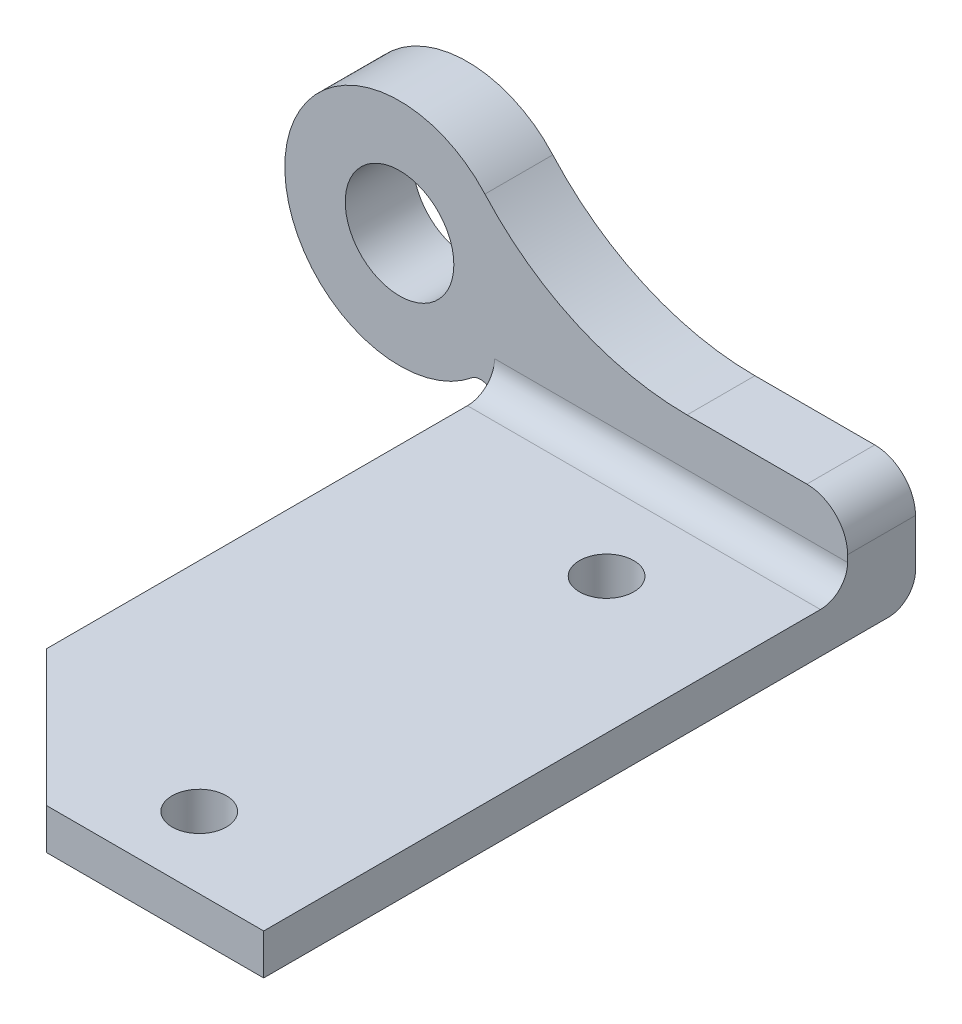
SolidWorks part; units mm, degrees
material "6061 合金"
ref_plane "前视基准面" through (0, 0, 0) normal (0, 0, 1) x (1, 0, 0)
ref_plane "上视基准面" through (0, 0, 0) normal (0, 1, 0) x (1, 0, 0)
ref_plane "右视基准面" through (0, 0, 0) normal (1, 0, 0) x (0, 0, -1)
sketch "草图1" plane through (0, 0, 0) normal (0, 0, 1) x (1, 0, 0)
  line L0 (-5.4584, -21.0602) -> (-5.4584, -21.2593)
  line L1 (-5.4584, -21.2593) -> (20.5416, -21.2593)
  line L2 (20.5416, -21.2593) -> (20.5416, -17.7593)
  line L3 (17.5416, -14.7593) -> (8.7172, -14.7593)
  line L4 (20.5416, -21.2593) -> (20.5416, -23.2593)
  line L5 (18.5416, -23.2593) -> (-3.4584, -23.2593)
  line L6 (-5.4584, -23.2593) -> (-3.4584, -23.2593)
  line L7 (-5.4584, -21.2593) -> (-5.4584, -23.2593)
  line L8 (18.5416, -23.2593) -> (20.5416, -23.2593)
  arc A0 (-5.4584, -21.0602) -> (-7.0933, -20.2876) centre (-6.4982, -21.1445) ccw
  arc A1 (20.5416, -17.7593) -> (17.5416, -14.7593) centre (17.5416, -17.7593) ccw
  arc A2 (-6.169, -8.1161) -> (8.7172, -14.7593) centre (8.7172, 5.2407) ccw
  arc A3 (-6.169, -8.1161) -> (-7.0933, -20.2876) centre (-12.4584, -13.7593) ccw
  arc A4 (-12.4584, -9.7593) -> (-12.4584, -17.7593) centre (-12.4584, -13.7593) ccw
  arc A5 (-12.4584, -17.7593) -> (-12.4584, -9.7593) centre (-12.4584, -13.7593) ccw
extrude "凸台-拉伸1" add sketch "草图1" along normal blind 3 and the other way blind 2 contours A2 A3 A0 L0 L1 L2 A1 L3 A5 A4 | L5 L8 L4 L1 L7 L6
sketch "草图2" plane through (0, -23.2593, 0) normal (0, -1, 0) x (1, 0, 0)
  line L0 (20.5416, 46.0048) -> (-5.4584, 46)
  line L3 (20.5416, -2) -> (-5.4584, -2)
  line L4 (-5.4584, 2) -> (-5.4584, -2)
  line L5 (-5.4584, 46) -> (-5.4584, 2)
  line L6 (1.5416, 7) -> (14.5416, 7) construction
  line L9 (20.5416, -2) -> (-5.4584, -2) construction
  line L10 (20.5416, 46.0048) -> (20.5416, -2)
  line L11 (20.5416, 3) -> (20.5416, -2) construction
  circle A6 centre (10.5416, 40.7504) radius 2
  circle A7 centre (10.5416, 10.7504) radius 2
  dimension "D3" = 4
  dimension "D4" = 4
  dimension "D1" = 26
  dimension "D2" = 9
  dimension "D5" = 13
  dimension "D6" = 7
extrude "凸台-拉伸2" add sketch "草图2" against normal blind 3
fillet "圆角1" radius 2 1 edges at (7.5416, -23.2593, -2)
chamfer "倒角1" distance 10 angle 45 1 edges at (-5.4584, -21.7593, 46)
fillet "圆角2" radius 2 1 edges at (7.5416, -20.2593, 3)
